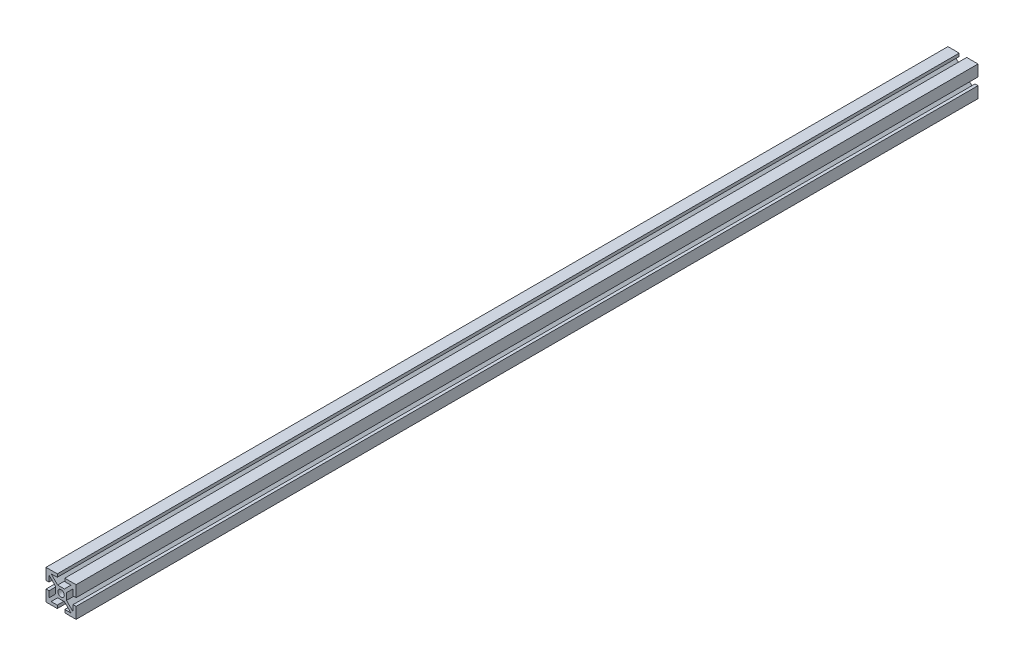
SolidWorks part; units mm, degrees
ref_plane "Plan de face" through (0, 0, 0) normal (0, 0, 1) x (1, 0, 0)
ref_plane "Plan de dessus" through (0, 0, 0) normal (0, 1, 0) x (1, 0, 0)
ref_plane "Plan de droite" through (0, 0, 0) normal (1, 0, 0) x (0, 0, -1)
sketch "Esquisse1" plane through (0, 0, 0) normal (0, 0, 1) x (1, 0, 0)
  line L0 (0, 0) -> (0, 68.6636) construction
  line L1 (-10, 10) -> (10, 10)
  line L2 (-10, 10) -> (-10, -10)
  line L3 (-10, -10) -> (10, -10)
  line L4 (10, 10) -> (10, -10)
  line L5 (-3.65, 3.65) -> (3.65, 3.65)
  line L6 (-3.65, 3.65) -> (-3.65, -3.65)
  line L7 (-3.65, -3.65) -> (3.65, -3.65)
  line L8 (3.65, 3.65) -> (3.65, -3.65)
  line L9 (0, 68.6636) -> (0, 0) construction
  line L10 (0, 0) -> (78.2836, 0) construction
  line L11 (-10, 10) -> (10, -10) construction
  line L12 (-2.5, 10) -> (2.5, 10)
  line L13 (-2.5, 10) -> (-2.5, 8)
  line L14 (-2.5, 8) -> (2.5, 8)
  line L15 (2.5, 10) -> (2.5, 8)
  line L16 (10, 2.5) -> (8, 2.5)
  line L17 (10, 2.5) -> (10, -2.5)
  line L18 (10, -2.5) -> (8, -2.5)
  line L19 (8, 2.5) -> (8, -2.5)
  line L20 (2.5, -10) -> (-2.5, -10)
  line L21 (2.5, -10) -> (2.5, -8)
  line L22 (2.5, -8) -> (-2.5, -8)
  line L23 (-2.5, -10) -> (-2.5, -8)
  line L24 (-10, -2.5) -> (-8, -2.5)
  line L25 (-10, -2.5) -> (-10, 2.5)
  line L26 (-10, 2.5) -> (-8, 2.5)
  line L27 (-8, -2.5) -> (-8, 2.5)
  line L28 (10, 10) -> (-10, -10) construction
  line L29 (-8, 2.5) -> (-8, 6.5858)
  line L30 (-8, 6.5858) -> (-3.65, 2.2358)
  line L31 (-3.65, 2.2358) -> (-3.65, -2.2358)
  line L32 (-3.65, -2.2358) -> (-8, -6.5858)
  line L33 (-8, -6.5858) -> (-8, -2.5)
  line L34 (-2.5, -8) -> (-6.5858, -8)
  line L35 (-6.5858, -8) -> (-2.2358, -3.65)
  line L36 (-2.2358, -3.65) -> (2.2358, -3.65)
  line L37 (2.2358, -3.65) -> (6.5858, -8)
  line L38 (6.5858, -8) -> (2.5, -8)
  line L39 (8, -6.5858) -> (3.65, -2.2358)
  line L40 (3.65, -2.2358) -> (3.65, 2.2358)
  line L41 (3.65, 2.2358) -> (8, 6.5858)
  line L42 (8, 6.5858) -> (8, 2.5)
  line L43 (8, 2.5) -> (8.0085, 2.747)
  line L44 (8, -2.5) -> (8, -6.5858)
  line L45 (2.5, 8) -> (6.5858, 8)
  line L46 (6.5858, 8) -> (2.2358, 3.65)
  line L47 (2.2358, 3.65) -> (-2.2358, 3.65)
  line L48 (-2.2358, 3.65) -> (-6.5858, 8)
  line L49 (-6.5858, 8) -> (-2.5, 8)
  circle A0 centre (0, 0) radius 2.15
  dimension "D1" = 4.3
  dimension "D2" = 6.35
  dimension "D3" = 6.35
  dimension "D4" = 6.35
  dimension "D5" = 6.35
  dimension "D6" = 20
  dimension "D7" = 20
  dimension "D8" = 5
  dimension "D9" = 5
  dimension "D10" = 5
  dimension "D11" = 5
  dimension "D12" = 2
  dimension "D13" = 2
  dimension "D14" = 2
  dimension "D15" = 2
  dimension "D16" = 2
  dimension "D17" = 2
  dimension "D18" = 2
  dimension "D19" = 2
extrude "Boss.-Extru.1" add sketch "Esquisse1" along normal blind 600
